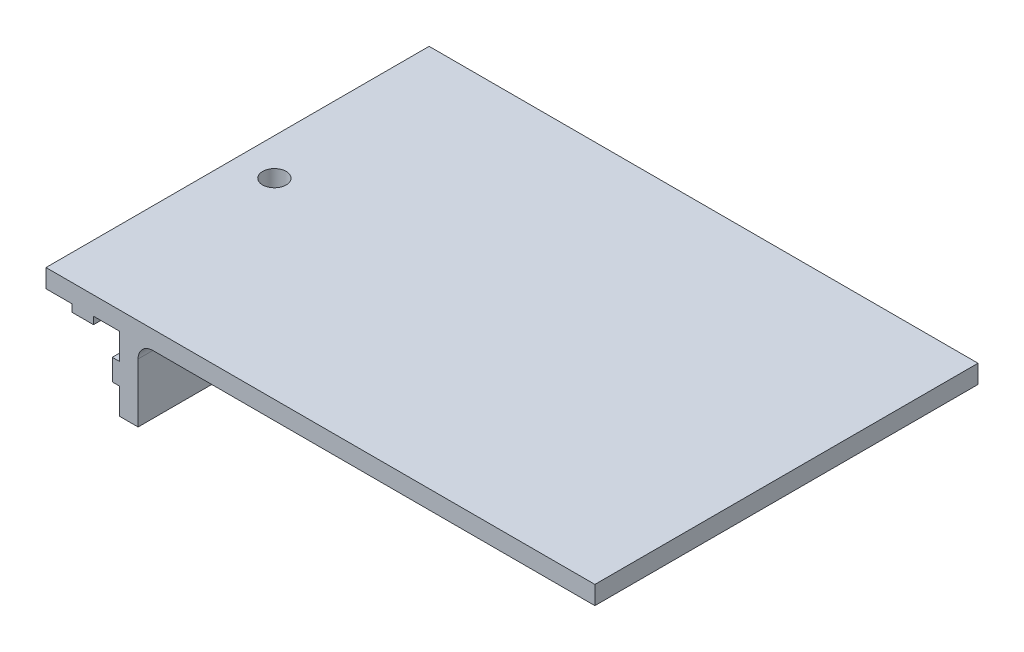
SolidWorks part; units mm, degrees
ref_plane "Front Plane" through (0, 0, 0) normal (0, 0, 1) x (1, 0, 0)
ref_plane "Top Plane" through (0, 0, 0) normal (0, 1, 0) x (1, 0, 0)
ref_plane "Right Plane" through (0, 0, 0) normal (1, 0, 0) x (0, 0, -1)
sketch "Sketch1" plane through (0, 0, 0) normal (0, 0, 1) x (1, 0, 0)
  line L0 (62, 0) -> (62, 2.5)
  line L1 (62, 2.5) -> (-12.5, 2.5)
  line L4 (-12.5, 2.5) -> (-12.5, 0)
  line L5 (-12.5, 0) -> (-8.95, 0)
  line L6 (-8.95, 0) -> (-8.95, -1)
  line L7 (-8.95, -1) -> (-6.05, -1)
  line L8 (-6.05, -1) -> (-6.05, 0)
  line L9 (-6.05, 0) -> (-2.5, 0)
  line L10 (-2.5, 0) -> (-2.5, -3.55)
  line L11 (-2.5, -3.55) -> (-3.5, -3.55)
  line L12 (-3.5, -3.55) -> (-3.5, -6.45)
  line L13 (-3.5, -6.45) -> (-2.5, -6.45)
  line L14 (-2.5, -6.45) -> (-2.5, -10)
  line L15 (-2.5, -10) -> (0, -10)
  line L16 (62, 0) -> (0, 0)
  line L17 (0, 0) -> (0, -10)
  point P3 (-7.2151, -2.356)
  point P4 (-19.989, 17.2938)
  point P6 (-5.7042, 13.2596)
  point P17 (-6.3978, 13.2596)
  point P19 (-6.3978, 15.3514)
  point P21 (-5.7042, 2.6726)
  point P22 (0, 0)
  point P23 (0, 0)
  point P24 (0, 0)
  point P25 (-7.4758, 12.5999)
  point P26 (-5.2877, 12.0894)
  point P27 (0, 0)
  dimension "D1" = 62
  dimension "D2" = 3.55
  dimension "D3" = 2.5
  dimension "D4" = 2.5
  dimension "D5" = 10
  dimension "D6" = 10
  dimension "D7" = 1
extrude "Boss-Extrude1" add sketch "Sketch1" along normal mid plane 52
fillet "Fillet1" radius 2 1 edges at (0, 0, 0)
sketch "Sketch2" plane through (0, 0, 0) normal (1, 0, 0) x (0, 0, -1)
  line L0 (-26, -10) -> (26, -10) construction
  circle A0 centre (0, -5) radius 1.6
  point P2 (0, -5.9842)
  point P5 (0, 0)
  dimension "D2" = 3.2
  dimension "D1" = 5
extrude "Cut-Extrude1" cut sketch "Sketch2" against normal through all
sketch "Sketch3" plane through (0, 2.5, 0) normal (0, 1, 0) x (1, 0, 0)
  line L0 (-12.5, -26) -> (-12.5, 26) construction
  circle A0 centre (-7.5, 0) radius 1.6
  point P2 (0, 0)
  dimension "D1" = 3.2
  dimension "D2" = 5
extrude "Cut-Extrude2" cut sketch "Sketch3" against normal through all
